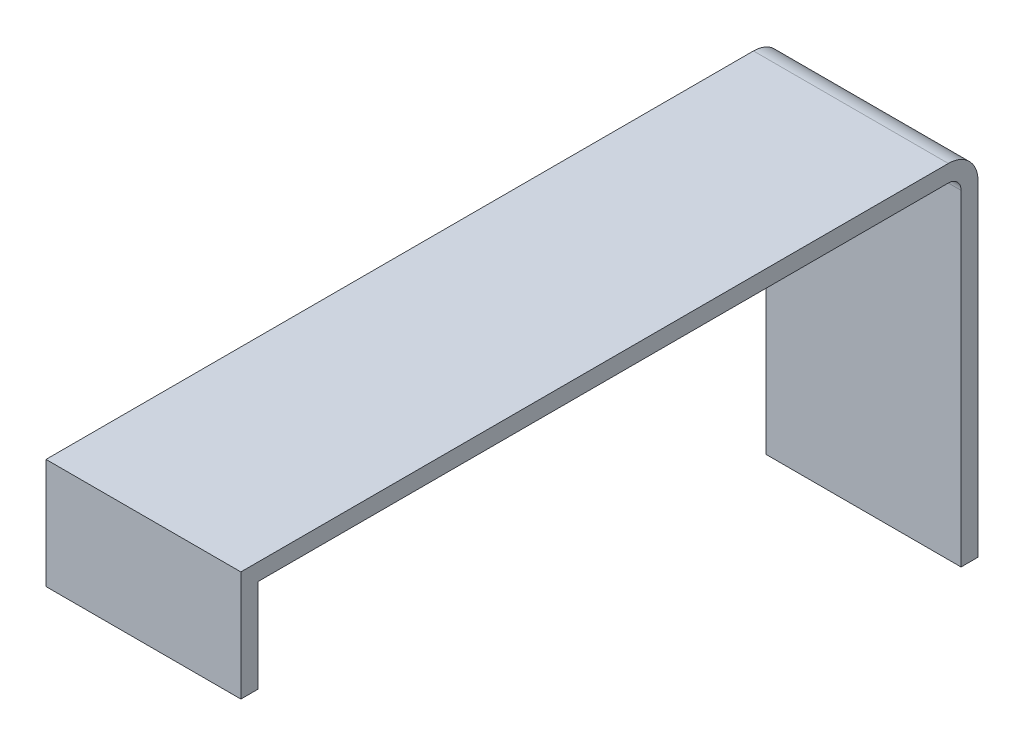
SolidWorks part; units mm, degrees
ref_plane "Front Plane" through (0, 0, 0) normal (0, 0, 1) x (1, 0, 0)
ref_plane "Top Plane" through (0, 0, 0) normal (0, 1, 0) x (1, 0, 0)
ref_plane "Right Plane" through (0, 0, 0) normal (1, 0, 0) x (0, 0, -1)
sketch "Sketch1" plane through (0, 0, 0) normal (0, 1, 0) x (1, 0, 0)
  line L1 (3.3071, 31.8366) -> (26.3071, 31.8366)
  line L2 (3.3071, 31.8366) -> (3.3071, -55.1634)
  line L3 (3.3071, -55.1634) -> (26.3071, -55.1634)
  line L4 (26.3071, 31.8366) -> (26.3071, -55.1634)
  dimension "D1" = 87
  dimension "D2" = 23
extrude "Boss-Extrude1" add sketch "Sketch1" along normal blind 42
fillet "Fillet1" radius 3.5 1 edges at (14.8071, 42, -31.8366)
sketch "Sketch2" plane through (26.3071, 0, 0) normal (1, 0, 0) x (0, 0, -1)
  line L8 (29.8366, 2) -> (29.8366, 38.5)
  line L9 (28.3366, 40) -> (-53.1634, 40)
  line L10 (-53.1634, 40) -> (-53.1634, 2)
  line L11 (-53.1634, 2) -> (29.8366, 2)
  line L12 (29.8366, 2) -> (29.8366, 38.5)
  line L13 (28.3366, 40) -> (-53.1634, 40)
  line L14 (-53.1634, 40) -> (-53.1634, 2)
  line L15 (-53.1634, 2) -> (29.8366, 2)
  arc A2 (29.8366, 38.5) -> (28.3366, 40) centre (28.3366, 38.5) ccw
  arc A3 (29.8366, 38.5) -> (28.3366, 40) centre (28.3366, 38.5) ccw
  dimension "D1" = 2
extrude "Cut-Extrude1" cut sketch "Sketch2" against normal through all
sketch "Sketch3" plane through (26.3071, 0, 0) normal (1, 0, 0) x (0, 0, -1)
  line L2 (-53.1634, 40) -> (-55.1634, 40)
  line L3 (-53.1634, 40) -> (-53.1634, 0)
  line L4 (-53.1634, 0) -> (-55.1634, 0)
  line L5 (-55.1634, 40) -> (-55.1634, 0)
extrude "Cut-Extrude3" cut sketch "Sketch3" against normal through all
sketch "Sketch4" plane through (26.3071, 0, 0) normal (1, 0, 0) x (0, 0, -1)
  line L0 (-53.1634, 0) -> (31.8366, 0) construction
  line L1 (-53.1634, 2) -> (29.8366, 2)
  line L2 (-53.1634, 2) -> (-53.1634, 0)
  line L3 (-53.1634, 0) -> (29.8366, 0)
  line L4 (29.8366, 2) -> (29.8366, 0)
extrude "Cut-Extrude5" cut sketch "Sketch4" against normal through all
sketch "Sketch6" plane through (0, 40, 0) normal (0, -1, 0) x (1, 0, 0)
  line L0 (26.3071, -28.3366) -> (26.3071, 55.1634) construction
  line L1 (3.3071, 55.1634) -> (26.3071, 55.1634)
  line L2 (3.3071, 55.1634) -> (3.3071, 53.1634)
  line L3 (3.3071, 53.1634) -> (26.3071, 53.1634)
  line L4 (26.3071, 55.1634) -> (26.3071, 53.1634)
  dimension "D1" = 2
extrude "Boss-Extrude2" add sketch "Sketch6" along normal blind 11
